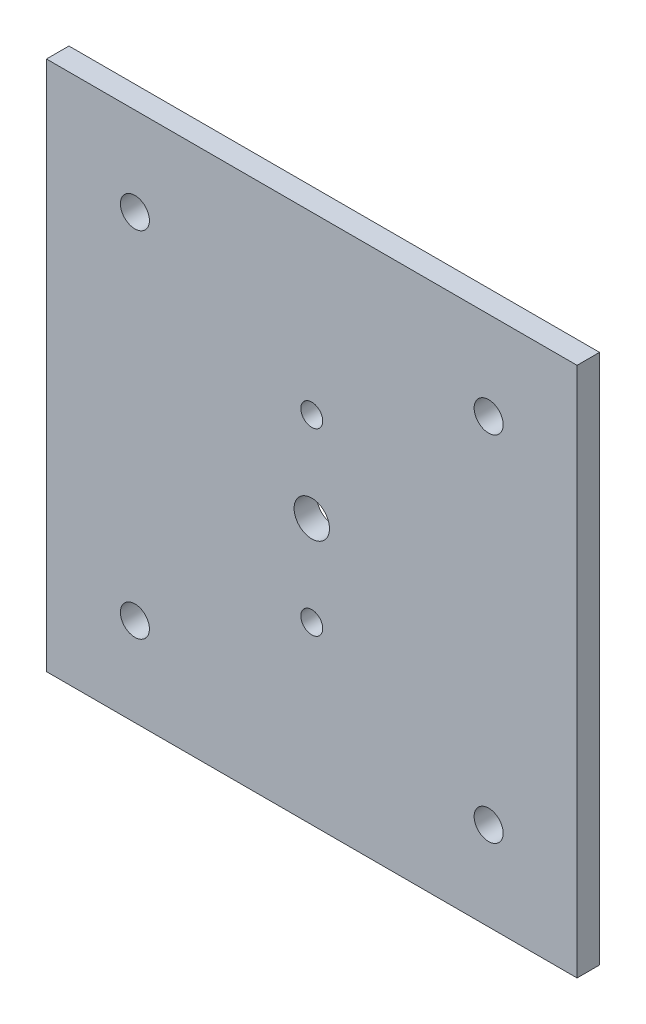
SolidWorks part; units mm, degrees
ref_plane "Front" through (0, 0, 0) normal (0, 0, 1) x (1, 0, 0)
ref_plane "Top" through (0, 0, 0) normal (0, 1, 0) x (1, 0, 0)
ref_plane "Right" through (0, 0, 0) normal (1, 0, 0) x (0, 0, -1)
sketch "Croquis1" plane through (0, 0, 0) normal (0, 0, 1) x (1, 0, 0)
  line L0 (0, 75) -> (0, -75) construction
  line L1 (-75, 75) -> (75, 75)
  line L2 (-75, 75) -> (-75, -75)
  line L3 (-75, -75) -> (75, -75)
  line L4 (75, 75) -> (75, -75)
  line L5 (-75, 75) -> (75, -75) construction
  line L6 (-75, -75) -> (75, 75) construction
  line L7 (-75, 0) -> (75, 0) construction
  line L8 (-50, 50) -> (50, 50) construction
  line L9 (50, 50) -> (50, -50) construction
  line L10 (50, -50) -> (-50, -50) construction
  line L11 (-50, -50) -> (-50, 50) construction
  circle A0 centre (0, 25.4) radius 3.1
  circle A1 centre (0, -25.4) radius 3.1
  circle A2 centre (-50, 50) radius 4.1
  circle A3 centre (50, 50) radius 4.1
  circle A4 centre (50, -50) radius 4.1
  circle A5 centre (-50, -50) radius 4.1
  circle A6 centre (0, 0) radius 5
  point P0 (0, 0)
  dimension "D3" = 6.2
  dimension "D4" = 6.2
  dimension "D7" = 8.2
  dimension "D8" = 8.2
  dimension "D9" = 8.2
  dimension "D10" = 8.2
  dimension "D15" = 10
  dimension "D1" = 150
  dimension "D2" = 150
  dimension "D5" = 50.8
  dimension "D6" = 25.4
  dimension "D11" = 100
  dimension "D12" = 100
  dimension "D13" = 50
  dimension "D14" = 50
extrude "Saliente-Extruir1" add sketch "Croquis1" along normal blind 6.35
